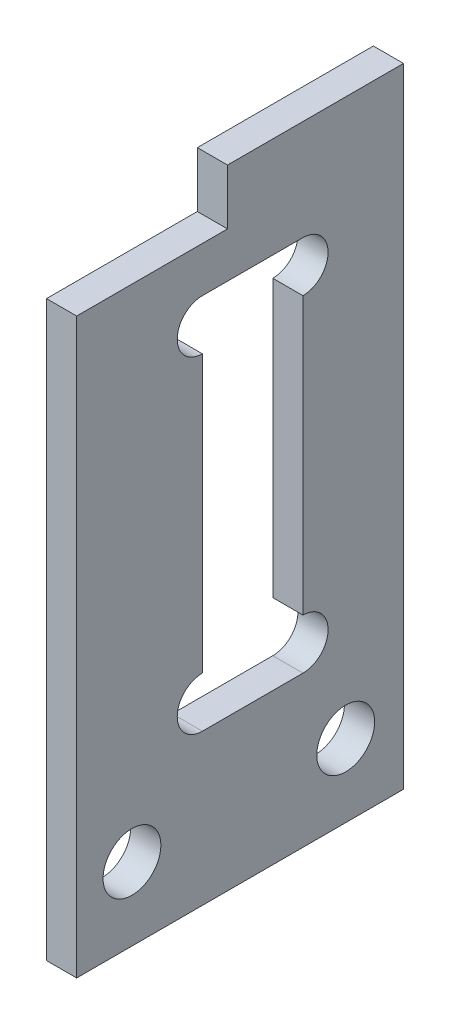
SolidWorks part; units mm, degrees
material "Легированная сталь"
ref_plane "Front" through (0, 0, 0) normal (0, 0, 1) x (1, 0, 0)
ref_plane "Top" through (0, 0, 0) normal (0, 1, 0) x (1, 0, 0)
ref_plane "Right" through (0, 0, 0) normal (1, 0, 0) x (0, 0, -1)
sketch "Эскиз1" plane through (0, 0, 0) normal (1, 0, 0) x (0, 0, -1)
  line L1 (0, 0) -> (15, 0)
  line L2 (0, 0) -> (0, 25)
  line L3 (0, 25) -> (15, 25)
  line L4 (15, 0) -> (15, 25)
  dimension "D1" = 25
  dimension "D2" = 15
extrude "Вытянуть1" add sketch "Эскиз1" along normal blind 1.2
sketch "Эскиз2" plane through (1.2, 0, 0) normal (1, 0, 0) x (0, 0, -1)
  line L0 (6, 25) -> (6, 22.8)
  line L1 (5, 6) -> (9, 6)
  line L2 (5, 8) -> (5, 19)
  line L3 (5, 21) -> (9, 21)
  line L4 (9, 8) -> (9, 19)
  line L5 (15, 0) -> (15, 25) construction
  line L6 (5, 6) -> (9, 21) construction
  line L7 (9, 6) -> (5, 21) construction
  line L8 (15, 25) -> (0, 25) construction
  line L9 (15, 0) -> (15, 25) construction
  line L10 (15, 22) -> (13, 22)
  line L11 (15, 22) -> (15, 5)
  line L12 (15, 5) -> (13, 5)
  line L13 (13, 22) -> (13, 5)
  line L14 (6, 22.8) -> (0, 22.8)
  line L15 (0, 25) -> (0, 0) construction
  line L16 (6, 25) -> (0, 25)
  line L17 (0, 25) -> (0, 22.8)
  arc A0 (5, 19) -> (5, 21) centre (5, 20) cw
  arc A1 (9, 19) -> (9, 21) centre (9, 20) ccw
  arc A2 (9, 8) -> (9, 6) centre (9, 7) cw
  arc A3 (5, 8) -> (5, 6) centre (5, 7) ccw
  circle A4 centre (10.7, 2.9) radius 1.15
  circle A5 centre (2.2, 2.9) radius 1.15
  point P6 (7, 13.5)
  dimension "D9" = 1
  dimension "D11" = 2.3
  dimension "D13" = 8.5
  dimension "D1" = 4
  dimension "D2" = 15
  dimension "D3" = 8
  dimension "D4" = 11.5
  dimension "D5" = 1
  dimension "D6" = 1.8
  dimension "D7" = 17
  dimension "D8" = 1
  dimension "D10" = 4
  dimension "D12" = 10.6
  dimension "D14" = 4.8
extrude "Вырез-Вытянуть1" cut sketch "Эскиз2" against normal up to next
sketch3d "Трехмерный эскиз1" [suppressed]
  line L0 (1.2, 20, -9) -> (1.2, 7, -5)
  line L1 (1.2, 20, -5) -> (1.2, 7, -9)
  arc A0 (1.2, 8, -5) -> (1.2, 6, -5) centre (1.2, 7, -5) ccw construction
  arc A1 (1.2, 6, -9) -> (1.2, 8, -9) centre (1.2, 7, -9) ccw construction
  arc A2 (1.2, 19, -9) -> (1.2, 21, -9) centre (1.2, 20, -9) ccw construction
  arc A3 (1.2, 21, -5) -> (1.2, 19, -5) centre (1.2, 20, -5) ccw construction
  point P8 (1.2, 13.5, -7)
  point P12 (2.2, 7, -5)
  point P16 (2.2, 7, -9)
  point P20 (2.2, 20, -9)
  point P24 (2.2, 20, -5)
sketch "Эскиз3" plane through (1.2, 0, 0) normal (1, 0, 0) x (0, 0, -1)
  line L0 (13, 5) -> (13, 0)
  line L1 (0, 0) -> (15, 0) construction
  line M13 (0, 0) -> (15, 0)
  line M14 (15, 0) -> (15, 5)
  line M15 (15, 5) -> (13, 5)
extrude "Вырез-Вытянуть2" cut sketch "Эскиз3" against normal through all contours L0 M15 M13 M14
sketch "Эскиз4" plane through (1.2, 0, 0) normal (1, 0, 0) x (0, 0, -1)
  line L0 (13, 22) -> (13, 25)
  line L1 (15, 25) -> (6, 25) construction
  line M13 (13, 22) -> (15, 22)
  line M14 (15, 22) -> (15, 25)
  line M15 (15, 25) -> (6, 25)
extrude "Вырез-Вытянуть3" cut sketch "Эскиз4" against normal through all contours L0 M13 M14 M15
